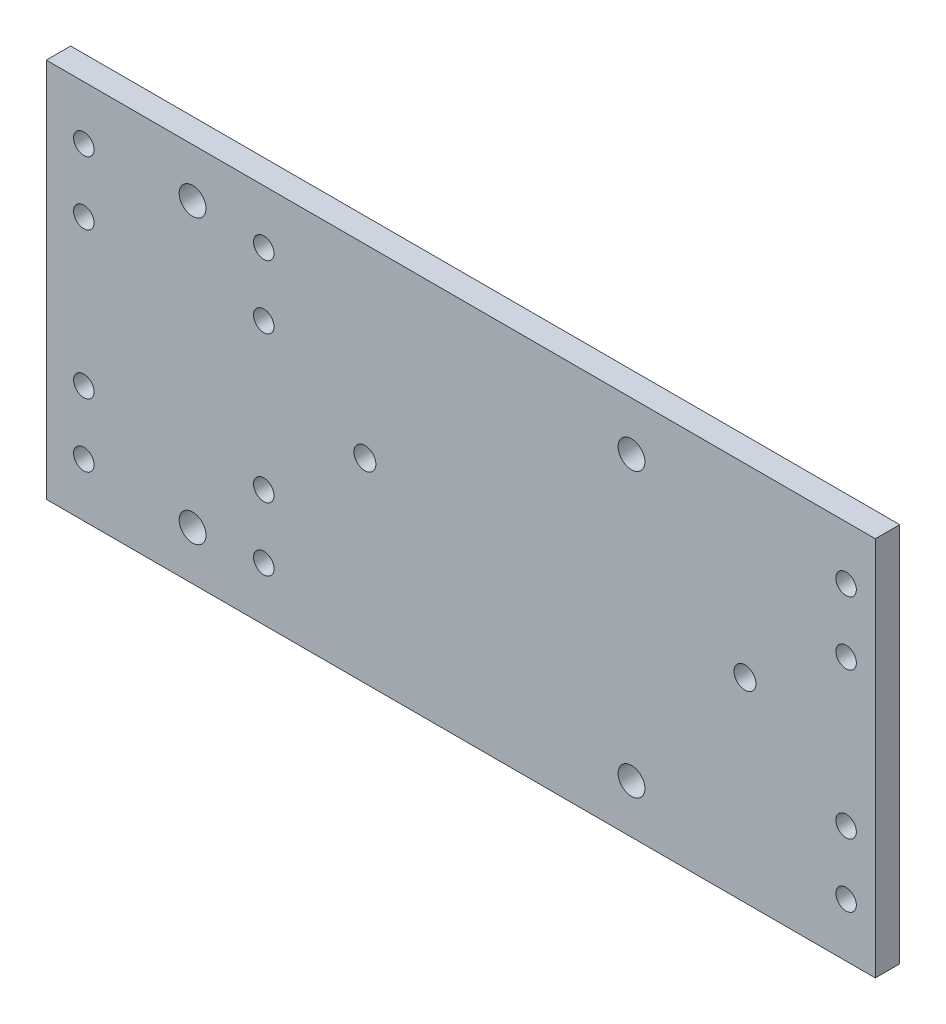
SolidWorks part; units mm, degrees
ref_plane "前视基准面" through (0, 0, 0) normal (0, 0, 1) x (1, 0, 0)
ref_plane "上视基准面" through (0, 0, 0) normal (0, 1, 0) x (1, 0, 0)
ref_plane "右视基准面" through (0, 0, 0) normal (1, 0, 0) x (0, 0, -1)
sketch "草图3" plane through (0, 0, 0) normal (0, 0, 1) x (1, 0, 0)
  line L0 (0, 78) -> (-170, 78)
  line L1 (0, 0) -> (0, 78)
  line L2 (-170, 0) -> (0, 0)
  line L3 (-170, 78) -> (-170, 0)
  line L4 (-143.025, 68) -> (-136.975, 68) construction
  line L5 (-140, 64.975) -> (-140, 71.025) construction
  line L6 (-53.025, 68) -> (-46.975, 68) construction
  line L7 (-50, 64.975) -> (-50, 71.025) construction
  line L8 (-143.025, 10) -> (-136.975, 10) construction
  line L9 (-140, 6.975) -> (-140, 13.025) construction
  line L10 (-53.025, 10) -> (-46.975, 10) construction
  line L11 (-50, 6.975) -> (-50, 13.025) construction
  line L12 (-29.2084, 40) -> (-24.2584, 40) construction
  line L13 (-26.7334, 37.525) -> (-26.7334, 42.475) construction
  line L14 (-107.1384, 40) -> (-102.1884, 40) construction
  line L15 (-104.6634, 37.525) -> (-104.6634, 42.475) construction
  circle A0 centre (-140, 68) radius 2.75
  circle A1 centre (-140, 10) radius 2.75
  circle A2 centre (-50, 10) radius 2.75
  circle A3 centre (-50, 68) radius 2.75
  circle A4 centre (-104.6634, 40) radius 2.25
  circle A5 centre (-26.7334, 40) radius 2.25
extrude "凸台-拉伸1" add sketch "草图3" along normal blind 5
hole_wizard "M5 螺纹孔1" positions "草图5" profile "草图6" tap size "M5" standard "ISO"
sketch "草图5" plane through (0, 0, 5) normal (0, 0, 1) x (1, 0, 0)
  line L0 (-170, 39) -> (0, 39) construction
  line L1 (-170, 78) -> (-170, 0) construction
  line L2 (0, 0) -> (0, 78) construction
  line L4 (0, 78) -> (-170, 78) construction
  point P0 (-162.3, 54)
  point P2 (-162.3, 67)
  point P13 (-162.3, 24)
  point P14 (-162.3, 11)
  dimension "D1" = 11
  dimension "D2" = 24
  dimension "D3" = 7.7
sketch "草图6" plane through (-162.3, 54, 5) normal (1, 0, 0) x (0, -1, 0)
  line L0 (0, 0) -> (0, 13.6618)
  line L1 (0, 13.6618) -> (2.1, 12.4)
  line L2 (2.1, 12.4) -> (2.1, 0)
  line L5 (2.1, 0) -> (0, 0)
  line L10 (0, 13.6618) -> (-2.1, 12.4) construction
  line L11 (0, -6.35) -> (0, 107.95) construction
  dimension "螺纹孔钻头直径" = 4.2
  dimension "螺纹孔钻头深度" = 12.4
  dimension "导头角度" = 118
cosmetic thread "孔螺蚊线1" parameters "D1"=5, "D2"=5
cosmetic thread "孔螺蚊线2" parameters "D1"=5, "D2"=5
cosmetic thread "孔螺蚊线3" parameters "D1"=5, "D2"=5
cosmetic thread "孔螺蚊线4" parameters "D1"=5, "D2"=5
pattern_linear "阵列(线性)1" count 2 spacing 36.9 along (1, 0, 0) of "M5 螺纹孔1"
pattern_linear "阵列(线性)2" count 2 spacing 156.3 along (1, 0, 0) of "M5 螺纹孔1"
